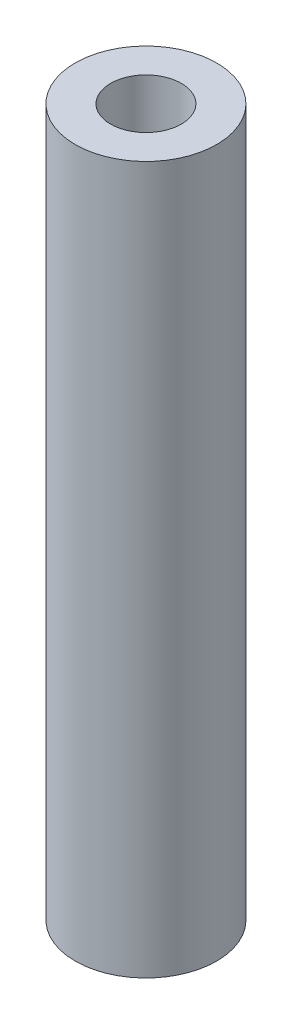
SolidWorks part; units mm, degrees
ref_plane "Front Plane" through (0, 0, 0) normal (0, 0, 1) x (1, 0, 0)
ref_plane "Top Plane" through (0, 0, 0) normal (0, 1, 0) x (1, 0, 0)
ref_plane "Right Plane" through (0, 0, 0) normal (1, 0, 0) x (0, 0, -1)
sketch "Croquis1" plane through (0, 0, 0) normal (0, 1, 0) x (1, 0, 0)
  circle A0 centre (0, 0) radius 0.5
  circle A1 centre (0, 0) radius 0.25
  dimension "D1" = 0.5
  dimension "D2" = 1
extrude "Saliente-Extruir1" add sketch "Croquis1" along normal blind 5
